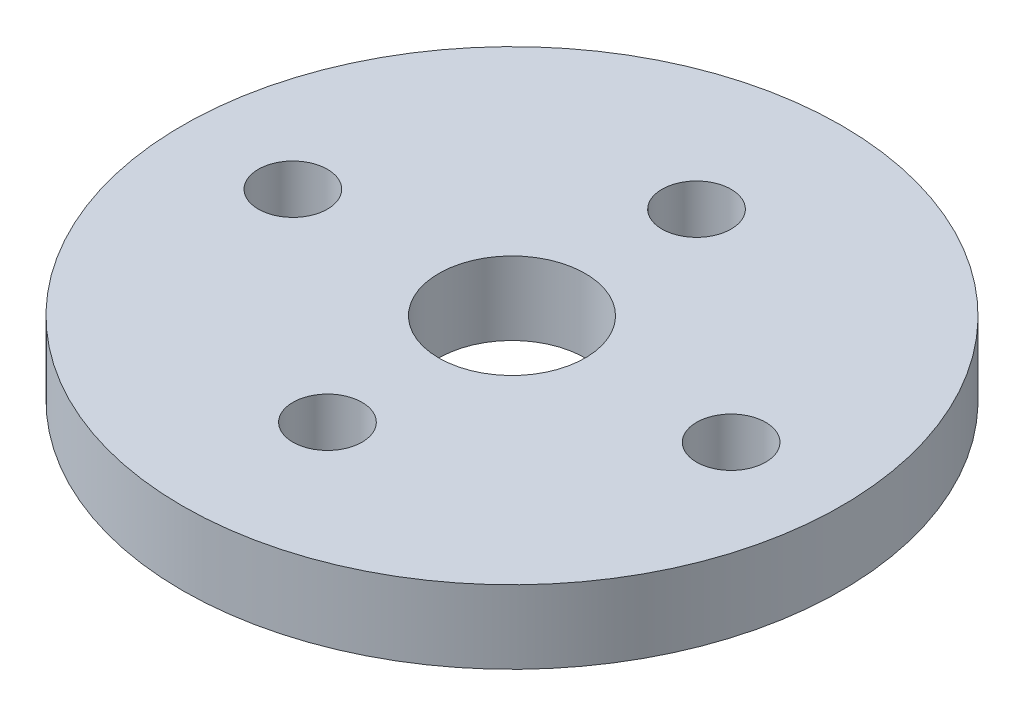
SolidWorks part; units mm, degrees
material "PLA/ABS"
ref_plane "Front Plane" through (0, 0, 0) normal (0, 0, 1) x (1, 0, 0)
ref_plane "Top Plane" through (0, 0, 0) normal (0, 1, 0) x (1, 0, 0)
ref_plane "Right Plane" through (0, 0, 0) normal (1, 0, 0) x (0, 0, -1)
other "Bounding Box"
ref_plane "Default Plane" through (13.8565, 3.175, 6.7999) normal (0, -1, 0) x (-1, 0, 0)
sketch "Sketch1" plane through (0, 0, 0) normal (0, 1, 0) x (1, 0, 0)
  line L0 (0, -8) -> (0, 8) construction
  line L1 (-9.5, 0) -> (9.5, 0) construction
  circle A0 centre (0, 0) radius 14.2875
  circle A1 centre (0, 8) radius 1.4986
  circle A2 centre (9.5, 0) radius 1.4986
  circle A3 centre (0, -8) radius 1.4986
  circle A4 centre (-9.5, 0) radius 1.4986
  circle A5 centre (0, 0) radius 3.175
  dimension "D3" = 2.9972
  dimension "D4" = 28.575
  dimension "D5" = 6.35
  dimension "D1" = 16
  dimension "D2" = 19
extrude "Boss-Extrude1" add sketch "Sketch1" along normal blind 3.175
